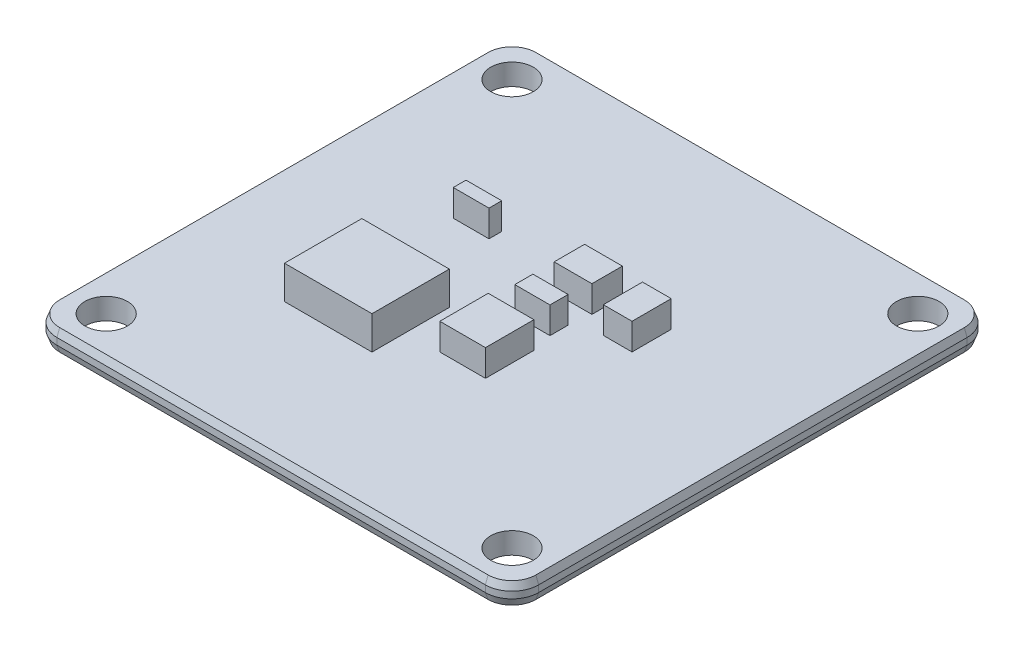
SolidWorks part; units mm, degrees
ref_plane "Plan de face" through (0, 0, 0) normal (0, 0, 1) x (1, 0, 0)
ref_plane "Plan de dessus" through (0, 0, 0) normal (0, 1, 0) x (1, 0, 0)
ref_plane "Plan de droite" through (0, 0, 0) normal (1, 0, 0) x (0, 0, -1)
sketch "Esquisse1" plane through (0, 0, 0) normal (0, 1, 0) x (1, 0, 0)
  line L0 (0, 0) -> (0, -33.9) construction
  line L1 (16.1, -18.1) -> (-16.1, -18.1)
  line L2 (18.1, -16.1) -> (18.1, 16.1)
  line L3 (16.1, 18.1) -> (-16.1, 18.1)
  line L4 (-18.1, -16.1) -> (-18.1, 16.1)
  line L5 (18.1, -18.1) -> (-18.1, 18.1) construction
  line L6 (18.1, 18.1) -> (-18.1, -18.1) construction
  arc A0 (16.1, -18.1) -> (18.1, -16.1) centre (16.1, -16.1) ccw
  arc A1 (-16.1, -18.1) -> (-18.1, -16.1) centre (-16.1, -16.1) cw
  arc A2 (-16.1, 18.1) -> (-18.1, 16.1) centre (-16.1, 16.1) ccw
  arc A3 (16.1, 18.1) -> (18.1, 16.1) centre (16.1, 16.1) cw
  circle A4 centre (-15.25, 15.25) radius 1.6
  circle A5 centre (15.25, 15.25) radius 1.6
  circle A6 centre (15.25, -15.25) radius 1.6
  circle A7 centre (-15.25, -15.25) radius 1.6
  point P0 (0, 0)
  point P27 (-15.6953, -18.1)
  dimension "D2" = 2
  dimension "D3" = 3.2
  dimension "D1" = 36.2
  dimension "D4" = 30.5
extrude "Boss.-Extru.1" add sketch "Esquisse1" along normal blind 1.6
chamfer "Chanfrein1" distance 0.2 angle 70 8 edges at (0, 1.6, 18.1) (17.5142, 1.6, 17.5142) (18.1, 1.6, 0) (17.5142, 1.6, -17.5142) (0, 1.6, -18.1) (-17.5142, 1.6, -17.5142) (-17.5142, 1.6, 17.5142) (-18.1, 1.6, 0)
chamfer "Chanfrein2" distance 0.2 angle 70 8 edges at (0, 0, 18.1) (17.5142, 0, 17.5142) (18.1, 0, 0) (17.5142, 0, -17.5142) (0, 0, -18.1) (-17.5142, 0, -17.5142) (-17.5142, 0, 17.5142) (-18.1, 0, 0)
sketch "Esquisse3" plane through (0, 1.6, 0) normal (0, 1, 0) x (1, 0, 0)
  circle A0 centre (-3.4774, -30.0062) radius 2.7849
  circle A1 centre (3.8108, -30.0062) radius 2.9073
sketch "Esquisse4" plane through (0, 1.6, 0) normal (0, 1, 0) x (1, 0, 0)
  line L1 (-9.3365, -1.949) -> (-2.7629, -1.949)
  line L2 (-9.3365, -1.949) -> (-9.3365, -7.7605)
  line L3 (-9.3365, -7.7605) -> (-2.7629, -7.7605)
  line L4 (-2.7629, -1.949) -> (-2.7629, -7.7605)
extrude "Boss.-Extru.2" add sketch "Esquisse4" along normal blind 2.5
sketch "Esquisse5" plane through (0, 1.6, 0) normal (0, 1, 0) x (1, 0, 0)
  line L1 (0.2091, 5.2472) -> (3.0487, 5.2472)
  line L2 (0.2091, 5.2472) -> (0.2091, 2.9575)
  line L3 (0.2091, 2.9575) -> (3.0487, 2.9575)
  line L4 (3.0487, 5.2472) -> (3.0487, 2.9575)
  line L5 (4.8437, 4.9658) -> (7.0016, 4.9658)
  line L6 (4.8437, 4.9658) -> (4.8437, 2.0198)
  line L7 (4.8437, 2.0198) -> (7.0016, 2.0198)
  line L8 (7.0016, 4.9658) -> (7.0016, 2.0198)
  line L9 (0.2091, 1.3631) -> (2.8548, 1.3631)
  line L10 (0.2091, 1.3631) -> (0.2091, 0)
  line L11 (0.2091, 0) -> (2.8548, 0)
  line L12 (2.8548, 1.3631) -> (2.8548, 0)
  line L13 (-0.2225, -1.564) -> (3.2113, -1.564)
  line L14 (-0.2225, -1.564) -> (-0.2225, -5.2042)
  line L15 (-0.2225, -5.2042) -> (3.2113, -5.2042)
  line L16 (3.2113, -1.564) -> (3.2113, -5.2042)
  line L17 (-8.4223, 4.9658) -> (-5.7391, 4.9658)
  line L18 (-8.4223, 4.9658) -> (-8.4223, 4.0088)
  line L19 (-8.4223, 4.0088) -> (-5.7391, 4.0088)
  line L20 (-5.7391, 4.9658) -> (-5.7391, 4.0088)
extrude "Boss.-Extru.3" add sketch "Esquisse5" along normal blind 2
